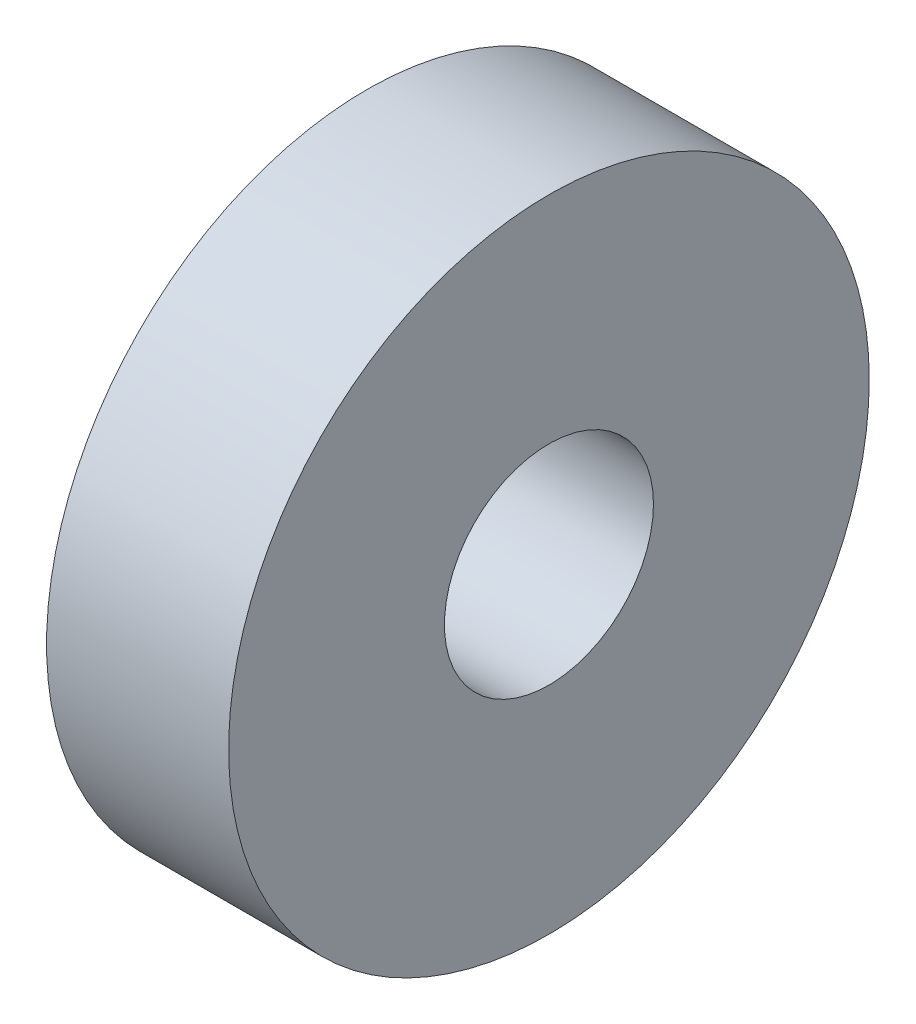
SolidWorks part; units mm, degrees
material "Brass"
ref_plane "Front Plane" through (0, 0, 0) normal (0, 0, 1) x (1, 0, 0)
ref_plane "Top Plane" through (0, 0, 0) normal (0, 1, 0) x (1, 0, 0)
ref_plane "Right Plane" through (0, 0, 0) normal (1, 0, 0) x (0, 0, -1)
sketch "Sketch1" plane through (0, 0, 0) normal (1, 0, 0) x (0, 0, -1)
  circle A0 centre (0, 0) radius 12.065
extrude "Boss-Extrude1" add sketch "Sketch1" along normal mid plane 6.858
sketch "Sketch2" plane through (3.429, 0, 0) normal (1, 0, 0) x (0, 0, -1)
  circle A0 centre (0, 0) radius 3.937
  circle A1 centre (0, 0) radius 12.065 construction
extrude "Cut-Extrude1" cut sketch "Sketch2" against normal through all
